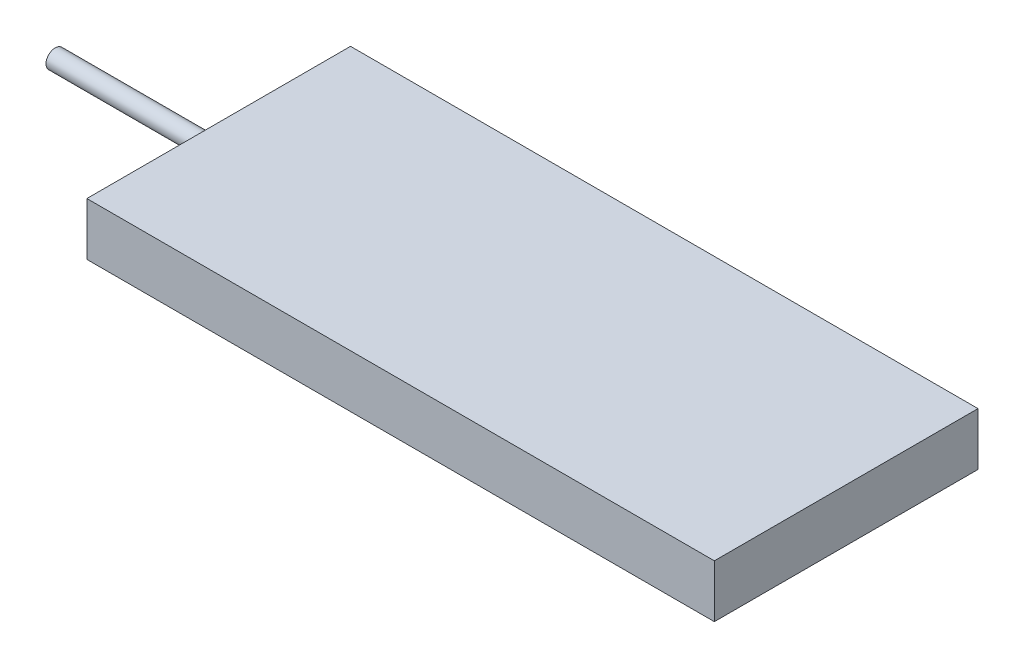
SolidWorks part; units mm, degrees
ref_plane "Front" through (0, 0, 0) normal (0, 0, 1) x (1, 0, 0)
ref_plane "Top" through (0, 0, 0) normal (0, 1, 0) x (1, 0, 0)
ref_plane "Right" through (0, 0, 0) normal (1, 0, 0) x (0, 0, -1)
sketch "草图1" plane through (0, 0, 0) normal (0, 1, 0) x (1, 0, 0)
  line L1 (0, 0) -> (238, 0)
  line L2 (0, 0) -> (0, 100)
  line L3 (0, 100) -> (238, 100)
  line L4 (238, 0) -> (238, 100)
  dimension "D1" = 100
  dimension "D2" = 238
extrude "凸台-拉伸2" add sketch "草图1" along normal blind 20 contours L3 L4 L1 L2
sketch "草图2" plane through (0, 0, 0) normal (-1, 0, 0) x (0, 0, 1)
  line L0 (0, 20) -> (-100, 20) construction
  line L1 (-100, 20) -> (-100, 0) construction
  circle A0 centre (-50, 10) radius 3.5
  dimension "D3" = 7
  dimension "D1" = 10
  dimension "D2" = 50
extrude "凸台-拉伸3" add sketch "草图2" along normal blind 62
other "3D 纹理2" [suppressed]
other "图形 (闭合) -2"
